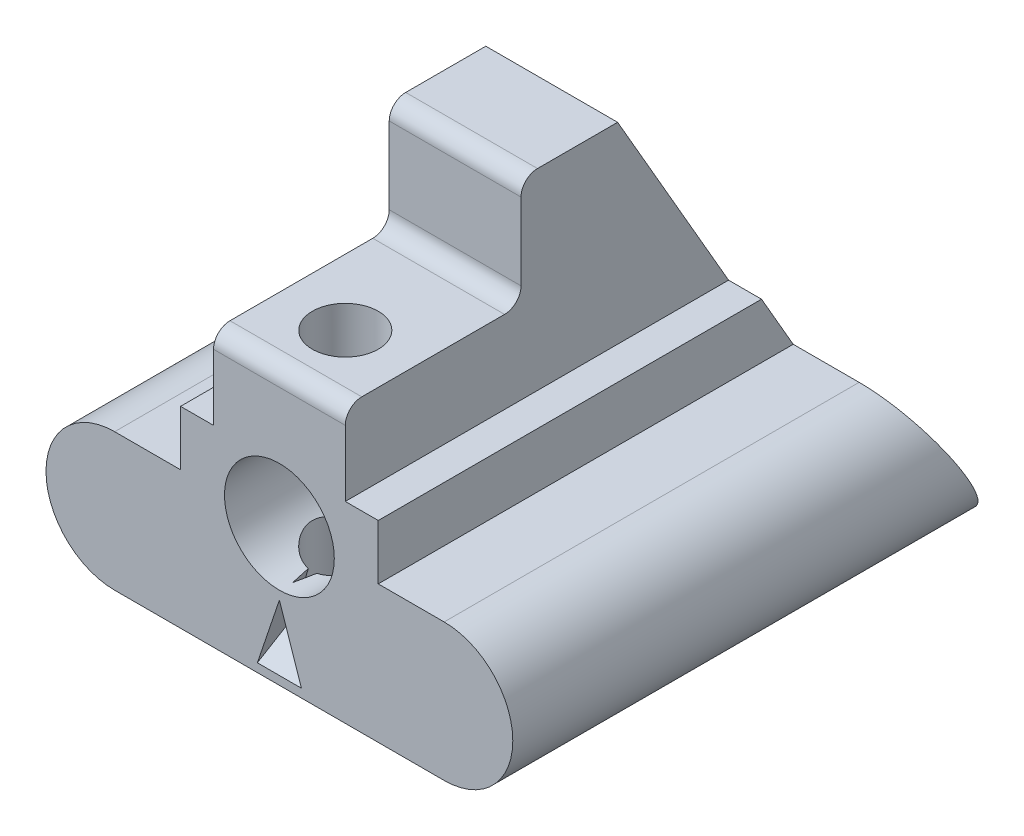
SolidWorks part; units mm, degrees
ref_plane "Front Plane" through (0, 0, 0) normal (0, 0, 1) x (1, 0, 0)
ref_plane "Top Plane" through (0, 0, 0) normal (0, 1, 0) x (1, 0, 0)
ref_plane "Right Plane" through (0, 0, 0) normal (1, 0, 0) x (0, 0, -1)
sketch "Sketch1" plane through (0, 0, 0) normal (0, 0, 1) x (1, 0, 0)
  line L0 (-30, 0) -> (30, 0) construction
  line L1 (-30, 12.5) -> (30, 12.5)
  line L2 (-30, -12.5) -> (30, -12.5)
  arc A0 (-30, 12.5) -> (-30, -12.5) centre (-30, 0) ccw
  arc A1 (30, -12.5) -> (30, 12.5) centre (30, 0) ccw
  point P2 (0, 0)
  dimension "D2" = 12.5
  dimension "D1" = 60
extrude "Boss-Extrude1" add sketch "Sketch1" along normal blind 90
ref_plane "Plane1" through (42.5, 0, 0) normal (1, 0, 0) x (0, 0, -1)
sketch "Sketch2" plane through (42.5, 0, 0) normal (1, 0, 0) x (0, 0, -1)
  line L0 (0, -12.5) -> (-14.4338, 12.5)
  line L1 (-90, 12.5) -> (0, 12.5) construction
  line L2 (-14.4338, 12.5) -> (0, 12.5)
  line L3 (0, 12.5) -> (0, -12.5)
  dimension "D1" = 30
extrude "Cut-Extrude1" cut sketch "Sketch2" against normal blind 90
sketch "Sketch3" plane through (0, 12.5, 0) normal (0, 1, 0) x (1, 0, 0)
  line L0 (18, -14.4338) -> (18, -90)
  line L1 (-30, -14.4338) -> (30, -14.4338) construction
  line L2 (30, -90) -> (-30, -90) construction
  line L3 (18, -90) -> (-18, -90)
  line L4 (-18, -90) -> (-18, -14.4338)
  line L5 (-18, -14.4338) -> (18, -14.4338)
  line L6 (30, -90) -> (30, -14.4338) construction
  line L7 (-30, -90) -> (-30, -14.4338) construction
  dimension "D1" = 12
  dimension "D2" = 12
extrude "Boss-Extrude2" add sketch "Sketch3" along normal blind 10
sketch "Sketch4" plane through (0, 22.5, 0) normal (0, 1, 0) x (1, 0, 0)
  line L0 (12, -90) -> (12, -14.4338)
  line L1 (-18, -90) -> (18, -90) construction
  line L2 (18, -14.4338) -> (-18, -14.4338) construction
  line L3 (12, -14.4338) -> (-12, -14.4338)
  line L4 (18, -14.4338) -> (-18, -14.4338) construction
  line L5 (-12, -14.4338) -> (-12, -90)
  line L6 (-12, -90) -> (12, -90)
  line L7 (18, -90) -> (18, -14.4338) construction
  line L8 (-18, -14.4338) -> (-18, -90) construction
  dimension "D1" = 6
  dimension "D2" = 6
extrude "Boss-Extrude3" add sketch "Sketch4" along normal blind 35
sketch "Sketch5" plane through (0, 57.5, 0) normal (0, 1, 0) x (1, 0, 0)
  line L0 (-12, -58) -> (12, -58)
  line L1 (-12, -14.4338) -> (-12, -90) construction
  line L2 (12, -90) -> (12, -14.4338) construction
  line L3 (12, -58) -> (12, -90)
  line L4 (12, -90) -> (-12, -90)
  line L5 (-12, -90) -> (-12, -58)
  dimension "D1" = 32
extrude "Cut-Extrude2" cut sketch "Sketch5" against normal blind 20
sketch "Sketch6" plane through (42.5, 0, 0) normal (1, 0, 0) x (0, 0, -1)
  line L0 (-14.4338, 12.5) -> (-40.4145, 57.5)
  line L1 (-58, 57.5) -> (-14.4338, 57.5) construction
  line L2 (-40.4145, 57.5) -> (-14.4338, 57.5)
  line L3 (-14.4338, 57.5) -> (-14.4338, 12.5)
  dimension "D1" = 30
extrude "Cut-Extrude3" cut sketch "Sketch6" against normal blind 440
sketch "Sketch9" plane through (0, 0, 90) normal (0, 0, 1) x (1, 0, 0)
  line L0 (-30, -12.5) -> (30, -12.5) construction
  circle A0 centre (0, 12.5) radius 10
  dimension "D2" = 20
  dimension "D1" = 25
  dimension "D3" = 30
extrude "Cut-Extrude6" cut sketch "Sketch9" against normal blind 440
sketch "Sketch11" plane through (0, 37.5, 0) normal (0, 1, 0) x (1, 0, 0)
  line L0 (12, -90) -> (12, -58) construction
  line L2 (-12, -90) -> (12, -90) construction
  circle A0 centre (0, -78) radius 6
  dimension "D1" = 12
  dimension "D2" = 12
  dimension "D3" = 12
extrude "Cut-Extrude7" cut sketch "Sketch11" against normal blind 440
sketch "Sketch12" plane through (-12, 0, 0) normal (-1, 0, 0) x (0, 0, 1)
  line L5 (55, 57.5) -> (58, 57.5)
  line L6 (58, 57.5) -> (58, 54.5)
  arc A0 (55, 57.5) -> (58, 54.5) centre (55, 54.5) cw
  point P10 (58, 57.5)
  dimension "D1" = 3
extrude "Cut-Extrude8" cut sketch "Sketch12" against normal blind 440
sketch "Sketch13" plane through (-12, 0, 0) normal (-1, 0, 0) x (0, 0, 1)
  line L5 (87, 37.5) -> (90, 37.5)
  line L6 (90, 37.5) -> (90, 34.5)
  arc A0 (90, 34.5) -> (87, 37.5) centre (87, 34.5) ccw
  point P10 (90, 37.5)
  dimension "D1" = 3
extrude "Cut-Extrude9" cut sketch "Sketch13" against normal blind 440
sketch "Sketch14" plane through (0, -3.125, 5.4127) normal (0, 0.5, -0.866) x (-1, 0, 0)
  line L0 (-6, 34.1747) -> (0, 49.1747)
  line L1 (0, 49.1747) -> (6, 34.1747)
  line L2 (6, 34.1747) -> (-6, 34.1747)
  line L3 (30, -10.8253) -> (-30, -10.8253) construction
  line L4 (12, 70.0037) -> (12, 29.5892) construction
  point P3 (0, 34.1747)
  dimension "D1" = 45
  dimension "D2" = 15
  dimension "D3" = 12
  dimension "D4" = 6
  dimension "D5" = 12
extrude "Cut-Extrude10" cut sketch "Sketch14" against normal blind 89 draft 1
sketch "Sketch16" plane through (12, 0, 0) normal (1, 0, 0) x (0, 0, -1)
  line L5 (-87, 37.5) -> (-58, 37.5) construction
  line L6 (-58, 37.5) -> (-58, 54.5) construction
  line L7 (-61, 37.5) -> (-58, 37.5)
  line L8 (-58, 37.5) -> (-58, 40.5)
  arc A0 (-61, 37.5) -> (-58, 40.5) centre (-61, 40.5) ccw
  point P10 (-58, 37.5)
  dimension "D1" = 3
extrude "Boss-Extrude4" add sketch "Sketch16" against normal blind 24
